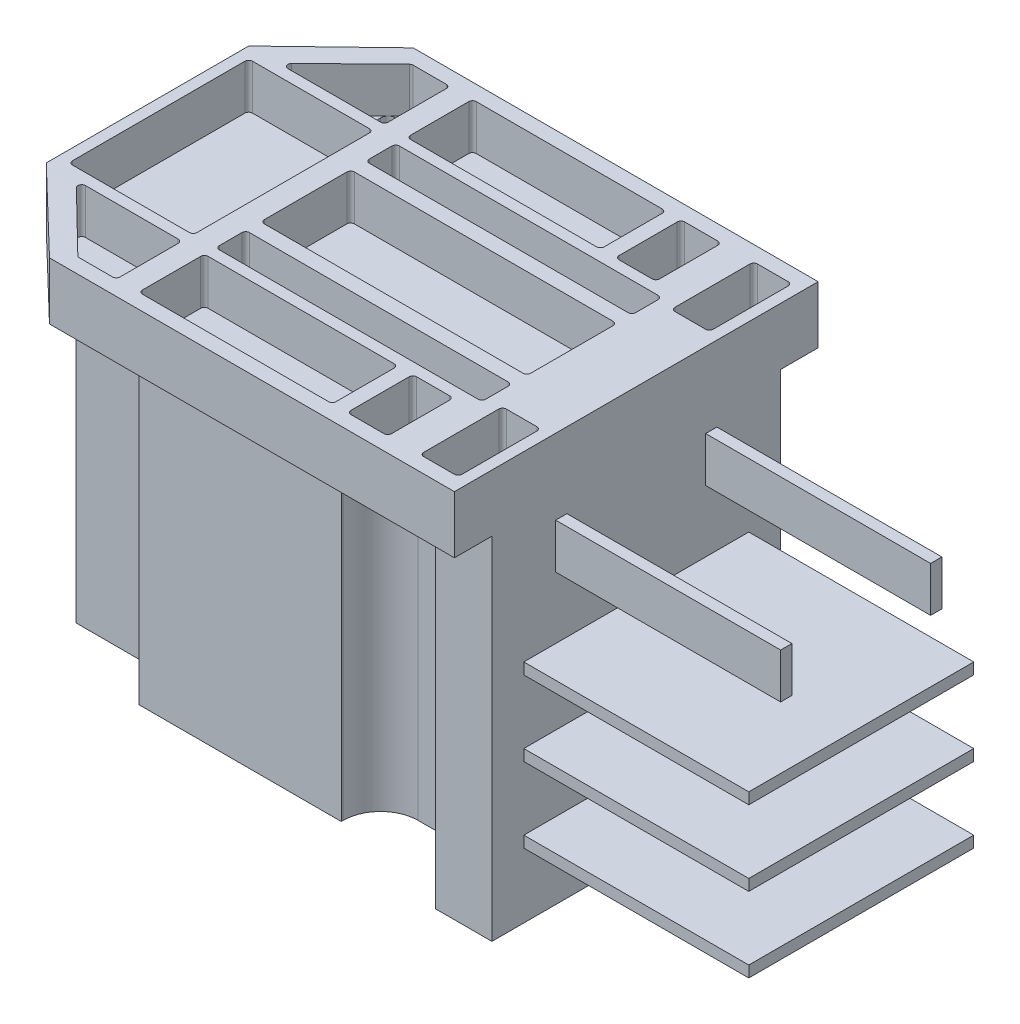
SolidWorks part; units mm, degrees
material "6061-T6 (SS)"
ref_plane "前视基准面" through (0, 0, 0) normal (0, 0, 1) x (1, 0, 0)
ref_plane "上视基准面" through (0, 0, 0) normal (0, 1, 0) x (1, 0, 0)
ref_plane "右视基准面" through (0, 0, 0) normal (1, 0, 0) x (0, 0, -1)
sketch "草图1" plane through (0, 0, 0) normal (0, 1, 0) x (1, 0, 0)
  line L1 (-32.59, 24.25) -> (32.59, 24.25)
  line L2 (-32.59, 24.25) -> (-32.59, -24.25)
  line L3 (-32.59, -24.25) -> (32.59, -24.25)
  line L4 (32.59, 24.25) -> (32.59, -24.25)
  line L5 (0, -24.25) -> (0, 24.25) construction
  line L6 (-32.59, 0) -> (32.59, 0) construction
  point P0 (0, 0)
  dimension "D1" = 48.5
  dimension "D2" = 65.18
extrude "凸台-拉伸1" add sketch "草图1" along normal blind 7.64
sketch "草图2" plane through (0, 7.64, 0) normal (0, 1, 0) x (1, 0, 0)
  line L0 (16.5, 21) -> (21.5, 21)
  line L1 (-19, 19) -> (19, 19) construction
  line L2 (-19, 19) -> (-19, -19) construction
  line L3 (-19, -19) -> (19, -19) construction
  line L4 (19, 19) -> (19, -19) construction
  line L5 (0, -19) -> (0, 19) construction
  line L6 (-19, 0) -> (19, 0) construction
  line L7 (-16.5, 17) -> (-21.5, 17)
  line L8 (-16.5, 17) -> (-16.5, 21)
  line L9 (-16.5, 21) -> (-21.5, 21)
  line L10 (-21.5, 17) -> (-21.5, 21)
  line L11 (-19, 21) -> (-19, 17) construction
  line L12 (-16.5, 19) -> (-21.5, 19) construction
  line L13 (21.5, 17) -> (21.5, 21)
  line L14 (16.5, 17) -> (21.5, 17)
  line L15 (16.5, 17) -> (16.5, 21)
  line L16 (16.5, -17) -> (16.5, -21)
  line L17 (16.5, -17) -> (21.5, -17)
  line L18 (21.5, -17) -> (21.5, -21)
  line L19 (16.5, -21) -> (21.5, -21)
  line L20 (-16.5, -21) -> (-21.5, -21)
  line L21 (-21.5, -17) -> (-21.5, -21)
  line L22 (-16.5, -17) -> (-21.5, -17)
  line L23 (-16.5, -17) -> (-16.5, -21)
  point P0 (0, 0)
  dimension "D2" = 5
  dimension "D1" = 38
  dimension "D3" = 4
extrude "切除-拉伸1" cut sketch "草图2" against normal through all
fillet "圆角1" radius 1 16 edges at (-21.5, 3.82, 21) (-16.5, 3.82, 21) (-16.5, 3.82, 17) (-21.5, 3.82, 17) (16.5, 3.82, 17) (16.5, 3.82, 21) (21.5, 3.82, 21) (21.5, 3.82, 17) (21.5, 3.82, -21) (16.5, 3.82, -21) (21.5, 3.82, -17) (16.5, 3.82, -17) (-21.5, 3.82, -17) (-21.5, 3.82, -21) (-16.5, 3.82, -21) (-16.5, 3.82, -17)
sketch "草图3" plane through (0, 7.64, 0) normal (0, 1, 0) x (1, 0, 0)
  line L0 (-21.41, 24.25) -> (-32.59, 13.5)
  line L1 (32.59, 24.25) -> (-32.59, 24.25) construction
  line L2 (-32.59, 24.25) -> (-32.59, -24.25) construction
  line L3 (-32.59, 0) -> (32.59, 0) construction
  line L4 (32.59, -24.25) -> (32.59, 24.25) construction
  line L5 (0, 24.25) -> (0, -24.25) construction
  line L6 (-32.59, -24.25) -> (32.59, -24.25) construction
  line L7 (-32.59, 13.5) -> (-32.59, 24.25)
  line L8 (-32.59, 24.25) -> (-21.41, 24.25)
  line L9 (-32.59, -13.5) -> (-32.59, -24.25)
  line L10 (-21.41, -24.25) -> (-32.59, -13.5)
  line L11 (-32.59, -24.25) -> (-21.41, -24.25)
  dimension "D1" = 13.5
  dimension "D2" = 54
extrude "切除-拉伸2" cut sketch "草图3" against normal through all
sketch "草图4" plane through (0, 0, 0) normal (0, -1, 0) x (1, 0, 0)
  line L0 (-32.59, 0) -> (32.59, 0) construction
  line L1 (-32.59, -13.5) -> (-32.59, 13.5) construction
  line L2 (32.59, 24.25) -> (32.59, -24.25) construction
  line L3 (-27.09, -15) -> (-27.09, 15)
  line L4 (-27.09, 15) -> (-13.5, 15)
  line L5 (-13.5, 15) -> (-13.5, 20.25)
  line L6 (-13.5, 20.25) -> (13.5, 20.25)
  line L7 (13.5, 20.25) -> (13.5, 15)
  line L8 (13.5, 15) -> (25.09, 15)
  line L9 (25.09, 15) -> (25.09, -15)
  line L10 (-17.5, 17) -> (-20.5, 17) construction
  line L11 (-16.5, 20) -> (-16.5, 18) construction
  line L12 (-21.41, 24.25) -> (32.59, 24.25) construction
  line L13 (16.5, 18) -> (16.5, 20) construction
  line L14 (20.5, 17) -> (17.5, 17) construction
  line L15 (13.5, -15) -> (25.09, -15)
  line L16 (13.5, -20.25) -> (13.5, -15)
  line L17 (-13.5, -20.25) -> (13.5, -20.25)
  line L18 (-13.5, -15) -> (-13.5, -20.25)
  line L19 (-27.09, -15) -> (-13.5, -15)
  point P25 (25.09, 0)
  point P30 (-27.09, 0)
  dimension "D1" = 2
  dimension "D2" = 5.5
  dimension "D3" = 3
  dimension "D4" = 4
  dimension "D5" = 3
  dimension "D6" = 2
  dimension "D7" = 7.5
extrude "凸台-拉伸2" add sketch "草图4" along normal blind 42
sketch "草图5" plane through (0, 0, 0) normal (0, -1, 0) x (1, 0, 0)
  line L0 (32.59, 24.25) -> (32.59, -24.25) construction
  line L1 (25.09, -15) -> (25.09, 15) construction
  line L2 (32.59, 19.25) -> (25.09, 19.25)
  line L3 (32.59, 19.25) -> (32.59, -19.25)
  line L4 (32.59, -19.25) -> (25.09, -19.25)
  line L5 (25.09, 19.25) -> (25.09, -19.25)
  line L6 (28.84, -19.25) -> (28.84, 19.25) construction
  line L7 (32.59, 0) -> (25.09, 0) construction
  line L8 (-27.09, 15) -> (-27.09, -15) construction
  line L9 (13.5, 20.25) -> (-13.5, 20.25) construction
  point P10 (-27.09, 0)
  point P598 (28.84, 0)
  dimension "D1" = 1
extrude "凸台-拉伸3" add sketch "草图5" along normal blind 46.8
fillet "圆角2" radius 5 4 edges at (-13.5, -21, 15) (13.5, -21, 15) (13.5, -21, -15) (-13.5, -21, -15)
sketch "草图6" plane through (32.59, 0, 0) normal (1, 0, 0) x (0, 0, -1)
  line L0 (0, -46.8) -> (0, 7.64) construction
  line L1 (19.25, -46.8) -> (-19.25, -46.8) construction
  line L2 (-24.25, 7.64) -> (24.25, 7.64) construction
  line L3 (-19.25, -23.4) -> (19.25, -23.4) construction
  line L4 (-19.25, -46.8) -> (-19.25, 0) construction
  line L5 (19.25, -46.8) -> (19.25, 0) construction
  line L6 (15, -28.15) -> (15, -26.65)
  line L7 (15, -18.15) -> (-15, -18.15)
  line L8 (15, -18.15) -> (15, -16.65)
  line L9 (15, -16.65) -> (-15, -16.65)
  line L10 (-15, -18.15) -> (-15, -16.65)
  line L11 (0, -16.65) -> (0, -18.15) construction
  line L12 (15, -17.4) -> (-15, -17.4) construction
  line L13 (15, -28.15) -> (-15, -28.15)
  line L14 (-15, -28.15) -> (-15, -26.65)
  line L15 (15, -26.65) -> (-15, -26.65)
  line L16 (15, -38.15) -> (15, -36.65)
  line L17 (15, -38.15) -> (-15, -38.15)
  line L18 (-15, -38.15) -> (-15, -36.65)
  line L19 (15, -36.65) -> (-15, -36.65)
  line L20 (15, -18.15) -> (15, -28.15) construction
  line L21 (9.25, -8.4) -> (10.75, -8.4)
  line L22 (-9.25, -2.4) -> (-10.75, -2.4)
  line L23 (-9.25, -2.4) -> (-9.25, -8.4)
  line L24 (-9.25, -8.4) -> (-10.75, -8.4)
  line L25 (-10.75, -2.4) -> (-10.75, -8.4)
  line L26 (-10, -8.4) -> (-10, -2.4) construction
  line L27 (-9.25, -5.4) -> (-10.75, -5.4) construction
  line L28 (10.75, -2.4) -> (10.75, -8.4)
  line L29 (9.25, -2.4) -> (10.75, -2.4)
  line L30 (9.25, -2.4) -> (9.25, -8.4)
  point P12 (0, -17.4)
  point P16 (-10, -5.4)
  dimension "D1" = 1.5
  dimension "D2" = 30
  dimension "D3" = 6
  dimension "D5" = 10
  dimension "D6" = 1.5
  dimension "D7" = 6
  dimension "D8" = 10
  dimension "D9" = 12
  dimension "D4" = 3
extrude "凸台-拉伸4" add sketch "草图6" along normal blind 30
sketch "草图8" plane through (0, 7.64, 0) normal (0, 1, 0) x (1, 0, 0)
  line L0 (-32.59, 0) -> (32.59, 0) construction
  line L1 (-32.59, 13.5) -> (-32.59, -13.5) construction
  line L2 (32.59, 15) -> (32.59, -15) construction
  line L3 (-28.59, 13.5) -> (-14.5, 13.5)
  line L4 (-14.5, 13.5) -> (-14.5, 22.25)
  line L5 (-14.5, 22.25) -> (-19.6267, 22.25)
  line L6 (-19.6267, 22.25) -> (-28.59, 13.5)
  line L7 (32.59, 24.25) -> (-21.41, 24.25) construction
  line L9 (-16.5, 18) -> (-16.5, 20) construction
  line L10 (-31.09, -12) -> (-31.09, 12)
  line L11 (-31.09, 12) -> (-14.5, 12)
  line L12 (-14.5, 12) -> (-14.5, -12)
  line L13 (16.5, 20) -> (16.5, 18) construction
  line L14 (16.3, 22.25) -> (21.7, 22.25)
  line L15 (16.3, 22.25) -> (16.3, 13.5)
  line L16 (16.3, 13.5) -> (21.7, 13.5)
  line L17 (21.7, 22.25) -> (21.7, 13.5)
  line L18 (19, 13.5) -> (19, 22.25) construction
  line L19 (16.3, 17.875) -> (21.7, 17.875) construction
  line L20 (21.5, 18) -> (21.5, 20) construction
  line L21 (-11.5, -6) -> (-11.5, 6)
  line L22 (-11.5, 22.25) -> (14.3, 22.25)
  line L23 (-11.5, 22.25) -> (-11.5, 13.5)
  line L24 (-11.5, 13.5) -> (14.3, 13.5)
  line L25 (14.3, 22.25) -> (14.3, 13.5)
  line L26 (1.4, 13.5) -> (1.4, 22.25) construction
  line L27 (-11.5, 17.875) -> (14.3, 17.875) construction
  line L28 (-11.5, 12) -> (24, 12)
  line L29 (-11.5, 12) -> (-11.5, 8)
  line L30 (-11.5, 8) -> (24, 8)
  line L31 (24, 12) -> (24, 8)
  line L32 (6.25, 8) -> (6.25, 12) construction
  line L33 (-11.5, 10) -> (24, 10) construction
  line L34 (-11.5, 6) -> (24, 6)
  line L35 (24, 6) -> (24, -6)
  line L36 (32.59, -24.25) -> (32.59, 24.25) construction
  line L37 (26, 22.25) -> (31.09, 22.25)
  line L38 (26, 22.25) -> (26, 11.25)
  line L39 (26, 11.25) -> (31.09, 11.25)
  line L40 (31.09, 22.25) -> (31.09, 11.25)
  line L41 (28.545, 11.25) -> (28.545, 22.25) construction
  line L42 (26, 16.75) -> (31.09, 16.75) construction
  line L43 (-11.5, -6) -> (24, -6)
  line L44 (-31.09, -12) -> (-14.5, -12)
  line L45 (26, -11.25) -> (31.09, -11.25)
  line L46 (31.09, -22.25) -> (31.09, -11.25)
  line L47 (26, -22.25) -> (31.09, -22.25)
  line L48 (26, -22.25) -> (26, -11.25)
  line L49 (16.3, -13.5) -> (21.7, -13.5)
  line L50 (21.7, -22.25) -> (21.7, -13.5)
  line L51 (16.3, -22.25) -> (21.7, -22.25)
  line L52 (16.3, -22.25) -> (16.3, -13.5)
  line L53 (-11.5, -8) -> (24, -8)
  line L54 (24, -12) -> (24, -8)
  line L55 (-11.5, -12) -> (24, -12)
  line L56 (-11.5, -12) -> (-11.5, -8)
  line L57 (-11.5, -13.5) -> (14.3, -13.5)
  line L58 (14.3, -22.25) -> (14.3, -13.5)
  line L59 (-11.5, -22.25) -> (14.3, -22.25)
  line L60 (-11.5, -22.25) -> (-11.5, -13.5)
  line L61 (-14.5, -22.25) -> (-19.6267, -22.25)
  line L62 (-14.5, -13.5) -> (-14.5, -22.25)
  line L63 (-28.59, -13.5) -> (-14.5, -13.5)
  line L64 (-19.6267, -22.25) -> (-28.59, -13.5)
  arc A0 (-20.5, 21) -> (-21.5, 20) centre (-20.5, 20) ccw construction
  point P49 (24, 0)
  point P50 (-11.5, 0)
  point P51 (-14.5, 0)
  point P52 (-31.09, 0)
  point P222 (1.4, 17.875)
  point P314 (19, 17.875)
  point P336 (28.545, 16.75)
  point P796 (6.25, 10)
  dimension "D1" = 4
  dimension "D2" = 2
  dimension "D3" = 2
  dimension "D4" = 1.5
  dimension "D5" = 1.5
  dimension "D6" = 0.2
  dimension "D7" = 0.2
  dimension "D8" = 3
  dimension "D9" = 2
  dimension "D10" = 35.5
  dimension "D11" = 4
  dimension "D12" = 2
  dimension "D13" = 2
  dimension "D14" = 1.5
  dimension "D15" = 11
extrude "切除-拉伸3" cut sketch "草图8" against normal blind 6
fillet "圆角3" radius 0.5 48 edges at (24, 4.64, 12) (24, 4.64, 8) (-11.5, 4.64, 8) (-11.5, 4.64, 12) (26, 4.64, -22.25) (31.09, 4.64, -22.25) (31.09, 4.64, -11.25) (26, 4.64, -11.25) (16.3, 4.64, -13.5) (16.3, 4.64, -22.25) (21.7, 4.64, -13.5) (21.7, 4.64, -22.25) (14.3, 4.64, -22.25) (14.3, 4.64, -13.5) (-11.5, 4.64, -13.5) (-11.5, 4.64, -22.25) (-11.5, 4.64, -12) (-11.5, 4.64, -8) (24, 4.64, -8) (24, 4.64, -12) (24, 4.64, -6) (-11.5, 4.64, -6) (-11.5, 4.64, 6) (24, 4.64, 6) (31.09, 4.64, 22.25) (31.09, 4.64, 11.25) (26, 4.64, 11.25) (26, 4.64, 22.25) (16.3, 4.64, 22.25) (16.3, 4.64, 13.5) (21.7, 4.64, 13.5) (21.7, 4.64, 22.25) (14.3, 4.64, 22.25) (14.3, 4.64, 13.5) (-11.5, 4.64, 13.5) (-11.5, 4.64, 22.25) (-19.6267, 4.64, 22.25) (-14.5, 4.64, 22.25) (-14.5, 4.64, 13.5) (-28.59, 4.64, 13.5) (-14.5, 4.64, -12) (-14.5, 4.64, 12) (-31.09, 4.64, 12) (-31.09, 4.64, -12) (-28.59, 4.64, -13.5) (-14.5, 4.64, -13.5) (-14.5, 4.64, -22.25) (-19.6267, 4.64, -22.25)
